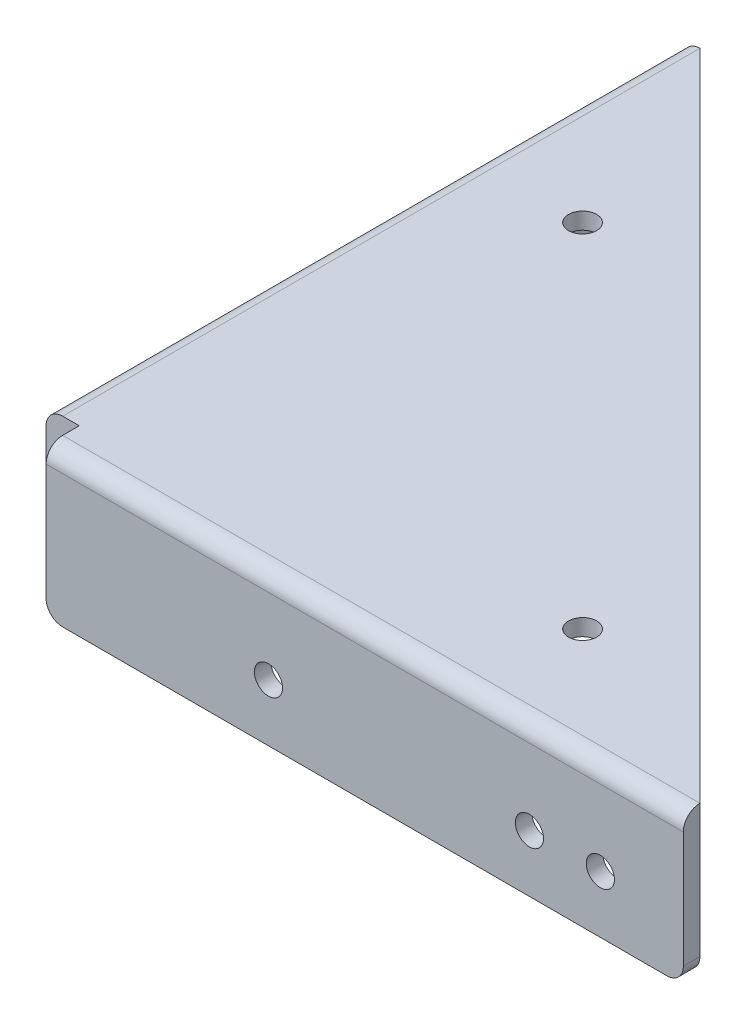
SolidWorks part; units mm, degrees
ref_plane "Front Plane" through (0, 0, 0) normal (0, 0, 1) x (1, 0, 0)
ref_plane "Top Plane" through (0, 0, 0) normal (0, 1, 0) x (1, 0, 0)
ref_plane "Right Plane" through (0, 0, 0) normal (1, 0, 0) x (0, 0, -1)
sketch "Sketch1" plane through (0, 0, 0) normal (0, 1, 0) x (1, 0, 0)
  line L0 (0, 0) -> (0, 102.616)
  line L1 (2.54, 102.616) -> (102.616, 2.54)
  line L2 (102.616, 0) -> (0, 0)
  line L3 (0, 102.616) -> (2.54, 102.616)
  line L4 (2.54, 102.616) -> (2.54, 2.54)
  line L5 (2.54, 2.54) -> (102.616, 2.54)
  line L6 (102.616, 2.54) -> (102.616, 0)
  dimension "D1" = 102.616
  dimension "D2" = 102.616
  dimension "D3" = 2.54
  dimension "D4" = 2.54
extrude "Boss-Extrude3" add sketch "Sketch1" along normal blind 22.86 contours L6 L5 L4 L3 L0 L2
sketch "Sketch3" plane through (0, 22.86, 0) normal (0, 1, 0) x (1, 0, 0)
  line L0 (2.54, 102.616) -> (102.616, 2.54)
  line L1 (102.616, 2.54) -> (2.54, 2.54)
  line L2 (2.54, 2.54) -> (2.54, 102.616)
extrude "Boss-Extrude4" add sketch "Sketch3" against normal blind 2.54
fillet "Fillet1" radius 2.54 5 edges at (0, 22.86, -51.308) (51.308, 22.86, 0) (2.54, 10.16, -2.54) (52.578, 20.32, -2.54) (2.54, 20.32, -52.578)
sketch "Sketch4" plane through (0, 20.32, 0) normal (0, -1, 0) x (1, 0, 0)
  line L0 (5.08, -5.08) -> (5.08, 2.1798)
  line L1 (5.08, 2.1798) -> (-2.9244, 2.1798)
  line L2 (-2.9244, 2.1798) -> (-2.9244, -5.08)
  line L3 (-2.9244, -5.08) -> (5.08, -5.08)
extrude "Cut-Extrude1" cut sketch "Sketch4" against normal blind 2.54 and the other way blind 32.004
hole_wizard "#8 Clearance Hole1" positions "Sketch6" profile "Sketch5" hole size "#8" standard "ANSI Inch"
sketch "Sketch6" plane through (2.54, 0, 0) normal (1, 0, 0) x (0, 0, -1)
  line L0 (102.616, 17.78) -> (102.616, 0) construction
  line L1 (102.616, 0) -> (5.08, 0) construction
  point P0 (39.116, 8.7312)
  point P2 (89.916, 8.7312)
  dimension "D1" = 12.7
  dimension "D2" = 8.7312
  dimension "D3" = 50.8
sketch "Sketch5" plane through (2.54, 8.7312, -39.116) normal (0, 1, 0) x (0, 0, -1)
  line L0 (0, 0) -> (0, 75.7154)
  line L1 (0, 75.7154) -> (2.1526, 74.422)
  line L2 (2.1526, 74.422) -> (2.1526, 0)
  line L5 (2.1526, 0) -> (0, 0)
  line L10 (0, 75.7154) -> (-2.1527, 74.422) construction
  line L11 (0, -6.35) -> (0, 107.95) construction
  dimension "Hole Dia." = 4.3053
  dimension "Hole Depth" = 74.422
  dimension "Drill Angle" = 118
hole_wizard "#8 Clearance Hole2" positions "Sketch8" profile "Sketch7" hole size "#8" standard "ANSI Inch"
sketch "Sketch8" plane through (0, 0, 0) normal (0, 0, 1) x (1, 0, 0)
  line L0 (102.616, 0) -> (5.08, 0) construction
  line L1 (102.616, 20.32) -> (102.616, 0) construction
  point P0 (89.916, 8.7312)
  point P2 (39.116, 8.7312)
  dimension "D1" = 8.7312
  dimension "D2" = 12.7
  dimension "D3" = 50.8
sketch "Sketch7" plane through (89.916, 8.7312, 0) normal (1, 0, 0) x (0, -1, 0)
  line L0 (0, 0) -> (0, 75.7154)
  line L1 (0, 75.7154) -> (2.1526, 74.422)
  line L2 (2.1526, 74.422) -> (2.1526, 0)
  line L5 (2.1526, 0) -> (0, 0)
  line L10 (0, 75.7154) -> (-2.1527, 74.422) construction
  line L11 (0, -6.35) -> (0, 107.95) construction
  dimension "Hole Dia." = 4.3053
  dimension "Hole Depth" = 74.422
  dimension "Drill Angle" = 118
hole_wizard "#8 Clearance Hole3" positions "Sketch10" profile "Sketch9" hole size "#8" standard "ANSI Inch"
sketch "Sketch10" plane through (0, 20.32, 0) normal (0, -1, 0) x (-1, 0, 0)
  line L0 (-16.657, 70.5385) -> (-30.2254, 84.107) construction
  line L1 (-70.5385, 16.657) -> (-88.4957, 34.6142) construction
  line L5 (-100.076, 5.08) -> (-5.08, 100.076) construction
  line L6 (-70.5385, 16.657) -> (-16.657, 70.5385) construction
  line L9 (-5.08, 100.076) -> (-100.076, 5.08) construction
  line L12 (-52.578, 52.578) -> (-43.5977, 43.5977) construction
  point P0 (-16.657, 70.5385)
  point P2 (-70.5385, 16.657)
  dimension "D1" = 76.2
  dimension "D2" = 90
  dimension "D3" = 12.7
  dimension "D4" = 12.7
sketch "Sketch9" plane through (16.657, 20.32, -70.5385) normal (1, 0, 0) x (0, 0, -1)
  line L0 (0, 0) -> (0, 75.7154)
  line L1 (0, 75.7154) -> (2.1526, 74.422)
  line L2 (2.1526, 74.422) -> (2.1526, 0)
  line L5 (2.1526, 0) -> (0, 0)
  line L10 (0, 75.7154) -> (-2.1527, 74.422) construction
  line L11 (0, -6.35) -> (0, 107.95) construction
  dimension "Hole Dia." = 4.3053
  dimension "Hole Depth" = 74.422
  dimension "Drill Angle" = 118
fillet "Fillet2" radius 2.54 4 edges at (1.27, 0, -102.616) (102.616, 0, -1.27) (1.27, 0, -5.08) (5.08, 0, -1.27)
sketch "Sketch11" plane through (2.54, 0, 0) normal (1, 0, 0) x (0, 0, -1)
  line L0 (79.0575, 8.7312) -> (89.916, 8.7312) construction
  circle A0 centre (79.0575, 8.7312) radius 2.159
  dimension "D2" = 4.318
  dimension "D1" = 10.8585
extrude "Cut-Extrude2" cut sketch "Sketch11" against normal blind 7.62
sketch "Sketch12" plane through (0, 0, 0) normal (0, 0, 1) x (1, 0, 0)
  line L0 (79.0575, 8.7313) -> (89.916, 8.7312) construction
  circle A0 centre (79.0575, 8.7313) radius 2.159
  dimension "D2" = 4.318
  dimension "D1" = 10.8585
extrude "Cut-Extrude3" cut sketch "Sketch12" against normal blind 7.62
